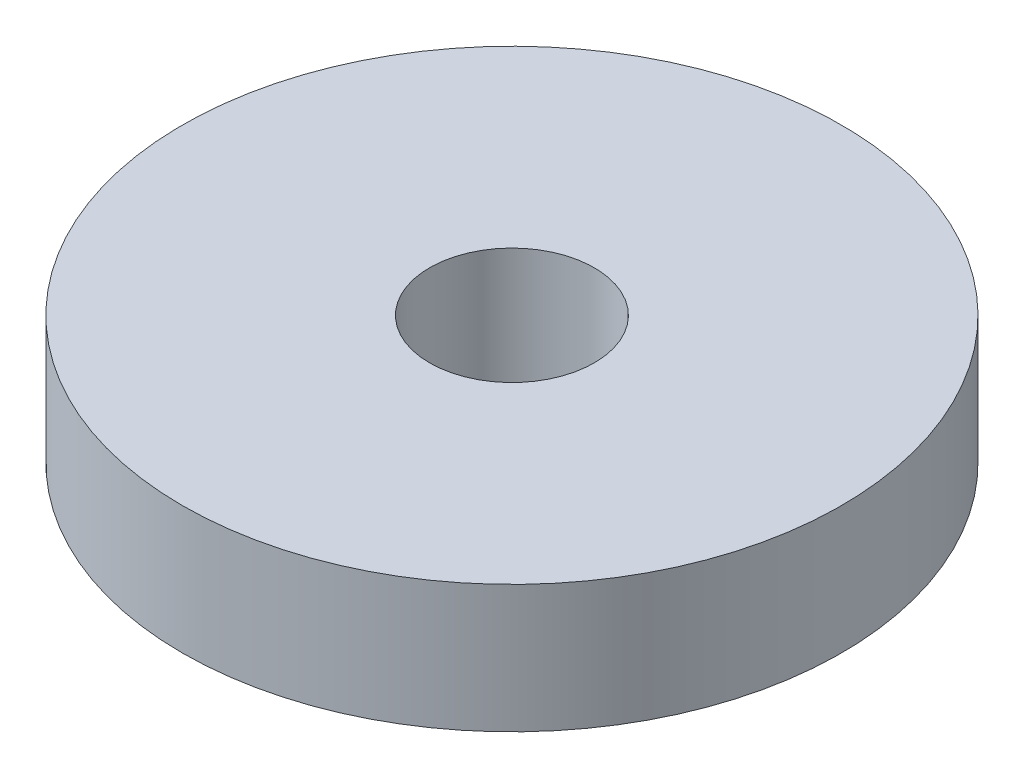
SolidWorks part; units mm, degrees
ref_plane "Front Plane" through (0, 0, 0) normal (0, 0, 1) x (1, 0, 0)
ref_plane "Top Plane" through (0, 0, 0) normal (0, 1, 0) x (1, 0, 0)
ref_plane "Right Plane" through (0, 0, 0) normal (1, 0, 0) x (0, 0, -1)
sketch "Sketch1" plane through (0, 0, 0) normal (0, 1, 0) x (1, 0, 0)
  circle A0 centre (0, 0) radius 2.54
  circle A1 centre (0, 0) radius 10.16
  dimension "D1" = 5.08
  dimension "D2" = 7.62
extrude "Boss-Extrude1" add sketch "Sketch1" along normal blind 3.937
